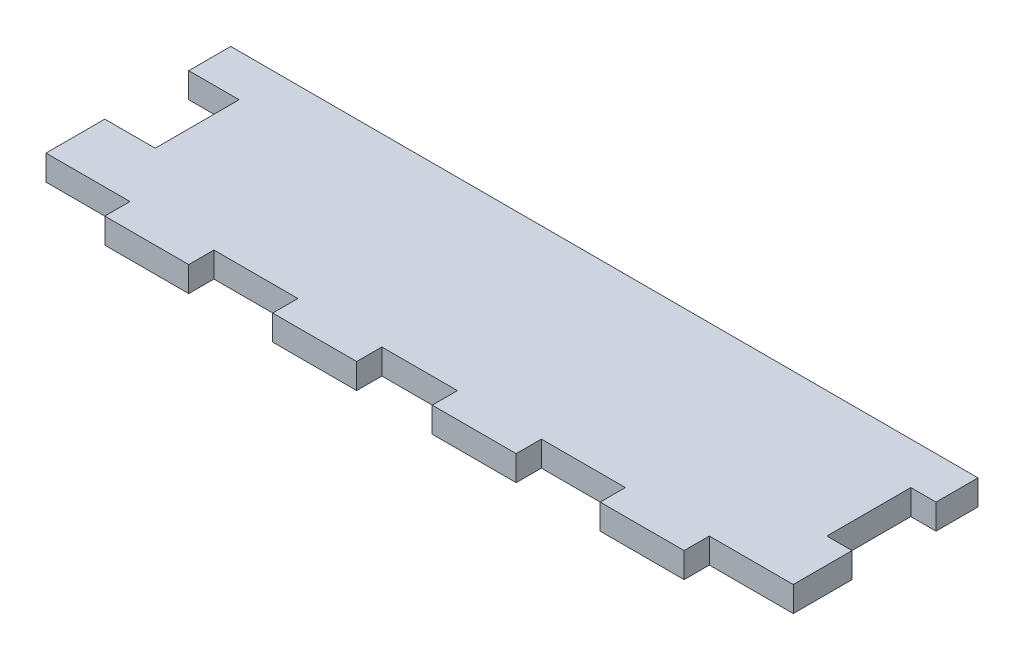
SolidWorks part; units mm, degrees
ref_plane "Front Plane" through (0, 0, 0) normal (0, 0, 1) x (1, 0, 0)
ref_plane "Top Plane" through (0, 0, 0) normal (0, 1, 0) x (1, 0, 0)
ref_plane "Right Plane" through (0, 0, 0) normal (1, 0, 0) x (0, 0, -1)
sketch "Sketch1" plane through (0, 0, 0) normal (0, 1, 0) x (1, 0, 0)
  line L0 (89, 17) -> (89, 22)
  line L1 (0, 0) -> (10, 0)
  line L2 (0, 0) -> (0, 7)
  line L3 (0, 22) -> (89, 22)
  line L4 (89, 0) -> (89, 7)
  line L5 (0, 17) -> (6, 17)
  line L6 (0, 22) -> (0, 17)
  line L7 (0, 7) -> (6, 7)
  line L8 (6, 17) -> (6, 7)
  line L9 (89, 17) -> (86, 17)
  line L10 (20, 0) -> (30, 0)
  line L11 (89, 7) -> (86, 7)
  line L12 (86, 17) -> (86, 7)
  line L14 (10, 0) -> (10, -3)
  line L15 (10, -3) -> (20, -3)
  line L16 (20, 0) -> (20, -3)
  line L18 (30, 0) -> (30, -3)
  line L19 (30, -3) -> (40, -3)
  line L20 (40, 0) -> (40, -3)
  line L22 (49, 0) -> (49, -3)
  line L23 (49, -3) -> (59, -3)
  line L24 (59, 0) -> (59, -3)
  line L26 (69, 0) -> (69, -3)
  line L27 (69, -3) -> (79, -3)
  line L28 (79, 0) -> (79, -3)
  line L29 (40, 0) -> (49, 0)
  line L30 (59, 0) -> (69, 0)
  line L31 (79, 0) -> (89, 0)
  dimension "D1" = 89
  dimension "D2" = 22
  dimension "D3" = 5
  dimension "D4" = 10
  dimension "D5" = 6
  dimension "D6" = 10
  dimension "D7" = 5
  dimension "D8" = 3
  dimension "D9" = 10
  dimension "D10" = 10
  dimension "D11" = 9
  dimension "D12" = 10
  dimension "D13" = 10
  dimension "D14" = 10
  dimension "D15" = 10
  dimension "D16" = 3
  dimension "D17" = 10
extrude "Boss-Extrude1" add sketch "Sketch1" along normal blind 3
